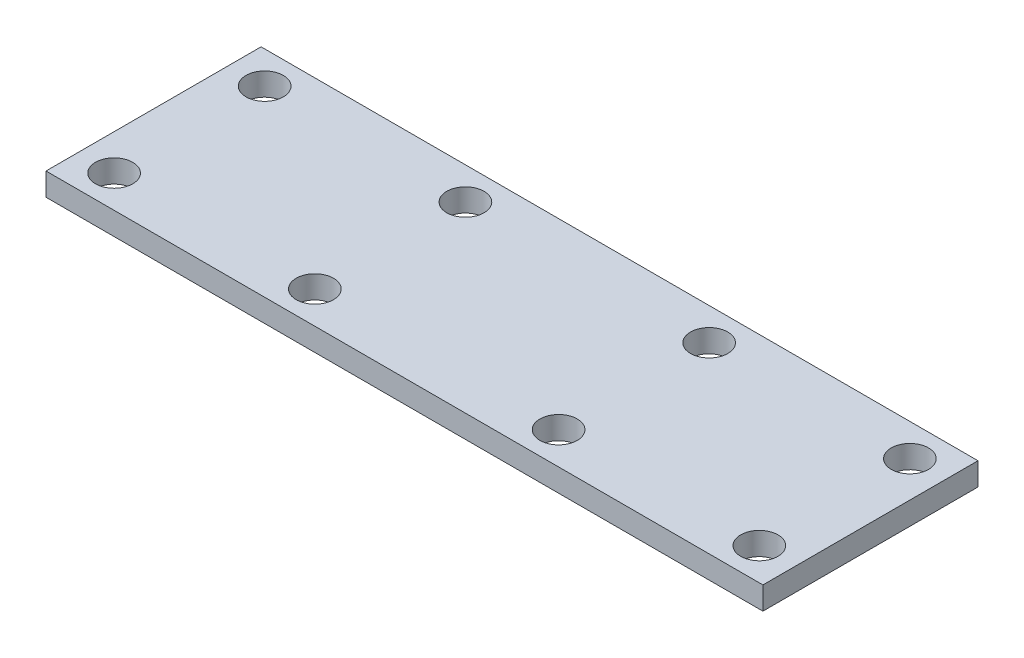
SolidWorks part; units mm, degrees
ref_plane "Front Plane" through (0, 0, 0) normal (0, 0, 1) x (1, 0, 0)
ref_plane "Top Plane" through (0, 0, 0) normal (0, 1, 0) x (1, 0, 0)
ref_plane "Right Plane" through (0, 0, 0) normal (1, 0, 0) x (0, 0, -1)
sketch "Sketch2" plane through (0, 0, 0) normal (0, 1, 0) x (1, 0, 0)
  line L0 (0, 28.8252) -> (0, -30.5208) construction
  line L1 (50, -15) -> (-50, -15)
  line L2 (50, -15) -> (50, 15)
  line L3 (50, 15) -> (-50, 15)
  line L4 (-50, -15) -> (-50, 15)
  line L5 (50, -15) -> (-50, 15) construction
  line L6 (50, 15) -> (-50, -15) construction
  line L7 (-55.3191, 0) -> (52.0088, 0) construction
  circle A0 centre (-17, 10.5) radius 2.6
  circle A1 centre (17, 10.5) radius 2.6
  circle A2 centre (17, -10.5) radius 2.6
  circle A3 centre (-17, -10.5) radius 2.6
  circle A4 centre (-45, 10.5) radius 2.6
  circle A5 centre (45, 10.5) radius 2.6
  circle A6 centre (45, -10.5) radius 2.6
  circle A7 centre (-45, -10.5) radius 2.6
  point P0 (0, 0)
  dimension "D1" = 90
  dimension "D5" = 100
  dimension "D2" = 4.5
  dimension "D3" = 34
  dimension "D4" = 21
  dimension "D6" = 30
extrude "Boss-Extrude1" add sketch "Sketch2" along normal blind 3.175
equation "\"D1@Boss-Extrude1\"=.125in"
